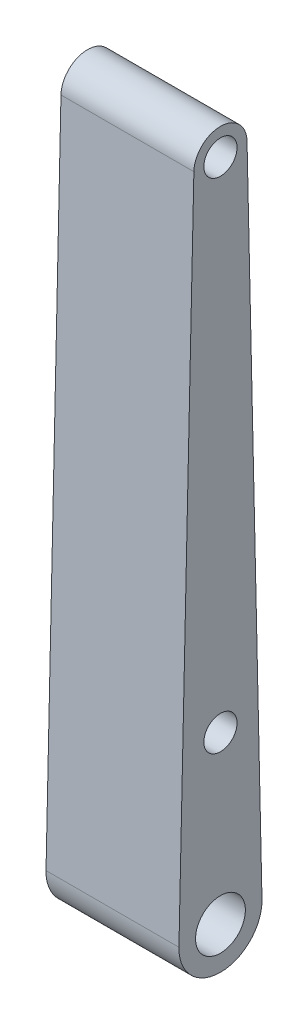
SolidWorks part; units mm, degrees
material "AISI 1020"
ref_plane "Front Plane" through (0, 0, 0) normal (0, 0, 1) x (1, 0, 0)
ref_plane "Top Plane" through (0, 0, 0) normal (0, 1, 0) x (1, 0, 0)
ref_plane "Right Plane" through (0, 0, 0) normal (1, 0, 0) x (0, 0, -1)
sketch "Sketch1" plane through (0, 0, 0) normal (1, 0, 0) x (0, 0, -1)
  line L2 (-5.0787, 127.1143) -> (-7.9355, 0.1786)
  line L4 (5.0787, 127.1143) -> (7.9355, 0.1786)
  circle A0 centre (0, 0) radius 4.7625
  arc A1 (-7.9355, 0.1786) -> (7.9355, 0.1786) centre (0, 0) ccw
  arc A3 (5.0787, 127.1143) -> (-5.0787, 127.1143) centre (0, 127) ccw
  point P3 (0, 0)
  dimension "D2" = 9.525
  dimension "D3" = 3.175
  dimension "D4" = 5.08
  dimension "D5" = 127
extrude "Boss-Extrude1" add sketch "Sketch1" along normal mid plane 25.4
sketch "Sketch2" plane through (12.7, 0, 0) normal (1, 0, 0) x (0, 0, -1)
  circle A0 centre (0, 31.75) radius 3.175
  circle A1 centre (0, 127) radius 3.175
  arc A2 (5.0787, 127.1143) -> (-5.0787, 127.1143) centre (0, 127) ccw construction
  dimension "D1" = 6.35
  dimension "D2" = 6.35
  dimension "D4" = 31.75
extrude "Cut-Extrude1" cut sketch "Sketch2" against normal through all
